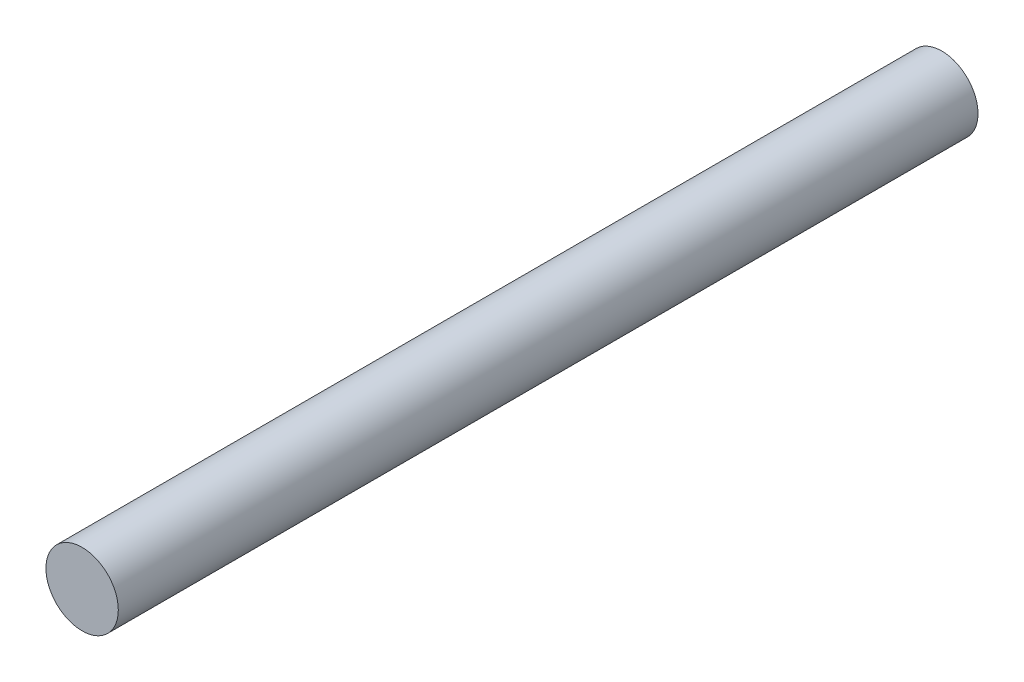
SolidWorks part; units mm, degrees
ref_plane "Front Plane" through (0, 0, 0) normal (0, 0, 1) x (1, 0, 0)
ref_plane "Top Plane" through (0, 0, 0) normal (0, 1, 0) x (1, 0, 0)
ref_plane "Right Plane" through (0, 0, 0) normal (1, 0, 0) x (0, 0, -1)
sketch "Sketch3" plane through (0, 0, 0) normal (0, 0, 1) x (1, 0, 0)
  circle A0 centre (0, 0) radius 78.35
  dimension "D1" = 156.7
extrude "Boss-Extrude1" add sketch "Sketch3" against normal blind 1861.1
